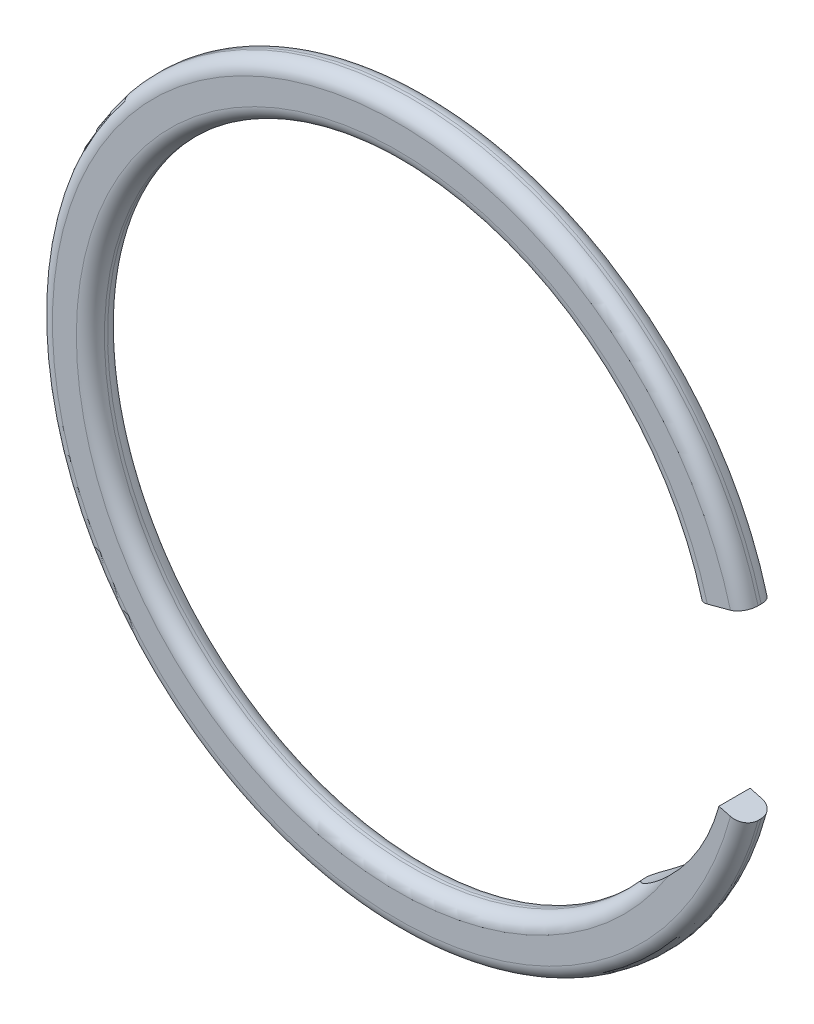
SolidWorks part; units mm, degrees
ref_plane "Front Plane" through (0, 0, 0) normal (0, 0, 1) x (1, 0, 0)
ref_plane "Top Plane" through (0, 0, 0) normal (0, 1, 0) x (1, 0, 0)
ref_plane "Right Plane" through (0, 0, 0) normal (1, 0, 0) x (0, 0, -1)
sketch "Sketch1" plane through (0, 0, 0) normal (0, 0, 1) x (1, 0, 0)
  line L0 (2.9972, 0) -> (3.5052, 0) construction
  line L1 (-2.9972, 0) -> (-3.5052, 0) construction
  line L2 (2.8951, 0.7757) -> (3.3858, 0.9072)
  line L3 (2.8951, -0.7757) -> (3.3858, -0.9072)
  line L4 (3.1404, -0.8415) -> (2.8014, -2.1068) construction
  line L5 (2.8014, -2.1068) -> (2.2648, -1.9631) construction
  circle A0 centre (0, 0) radius 2.9972
  circle A1 centre (0, 0) radius 3.5052
  arc A2 (3.1404, -0.8415) -> (2.2648, -1.9631) centre (1.38, -0.3698) cw
  dimension "Free Diameter" = 5.9944
  dimension "Radial Wall" = 0.508
  dimension "D3" = 30
sketch "Sketch2" plane through (0, 0, 0) normal (0, 0, 1) x (1, 0, 0)
  line L0 (2.8951, -0.7757) -> (3.3858, -0.9072) construction
  line L1 (2.8951, 0.7757) -> (3.3858, 0.9072) construction
  line L2 (3.1404, -0.8415) -> (3.3858, -0.9072)
  line L3 (2.8951, 0.7757) -> (3.3858, 0.9072)
  circle A0 centre (0, 0) radius 3.5052 construction
  arc A1 (2.2648, -1.9631) -> (3.1404, -0.8415) centre (1.38, -0.3698) ccw construction
  circle A2 centre (0, 0) radius 2.9972 construction
  arc A3 (3.3858, 0.9072) -> (3.3858, -0.9072) centre (0, 0) ccw
  arc A4 (2.2648, -1.9631) -> (3.1404, -0.8415) centre (1.38, -0.3698) ccw
  arc A5 (2.8951, 0.7757) -> (2.2648, -1.9631) centre (0, 0) ccw
  arc A6 (2.8951, 0.7757) -> (2.2648, -1.9631) centre (0, 0) cw construction
  arc A7 (3.3858, 0.9072) -> (3.3858, -0.9072) centre (0, 0) cw construction
extrude "Extrude1" add sketch "Sketch2" along normal mid plane 0.3048
fillet "Fillet1" radius 0.1372 4 edges at (-3.5052, 0, -0.1524) (-3.5052, 0, 0.1524) (-2.9209, 0.6721, -0.1524) (-2.9209, 0.6721, 0.1524)
sketch "Sketch3" plane through (0, 0, 0) normal (1, 0, 0) x (0, 0, -1)
  line L0 (-0.1905, 3.175) -> (-0.1905, 3.0226)
  line L1 (-0.1905, 3.0226) -> (0.1905, 3.0226)
  line L2 (0.1905, 3.0226) -> (0.1905, 3.175)
  line L3 (0.1905, 3.175) -> (8.3344, 3.175)
  line L4 (8.3344, 3.175) -> (8.3344, 0)
  line L5 (-0.1905, 3.175) -> (-0.7144, 3.175)
  line L6 (-0.7144, 3.175) -> (-1.1906, 2.6987)
  line L7 (-1.1906, 2.6987) -> (-1.1906, 0)
  line L8 (-1.1906, 0) -> (8.3344, 0)
  line L9 (-1.1906, 0) -> (8.3344, 0) construction
  line L10 (0, 0) -> (0, 3.0226) construction
  dimension "Groove width" = 0.381
  dimension "groove dia" = 6.0452
  dimension "shaft dia" = 6.35
  dimension "D1" = 45
  dimension "D2" = 5.3975
  dimension "D3" = 9.525
  dimension "D4" = 1.1906
revolve "Revolve1" [suppressed] add sketch "Sketch3" angle 360 about L8
equation "\"D1@Fillet1\" = (\"Ring Thickness@Extrude1\"*.9)/2"
equation "\"D2@Sketch3\" = \"shaft dia@Sketch3\"*.85"
equation "\"D4@Sketch3\" = \"D3@Sketch3\"/8"
equation "\"D3@Sketch3\" = \"shaft dia@Sketch3\"*1.50"
